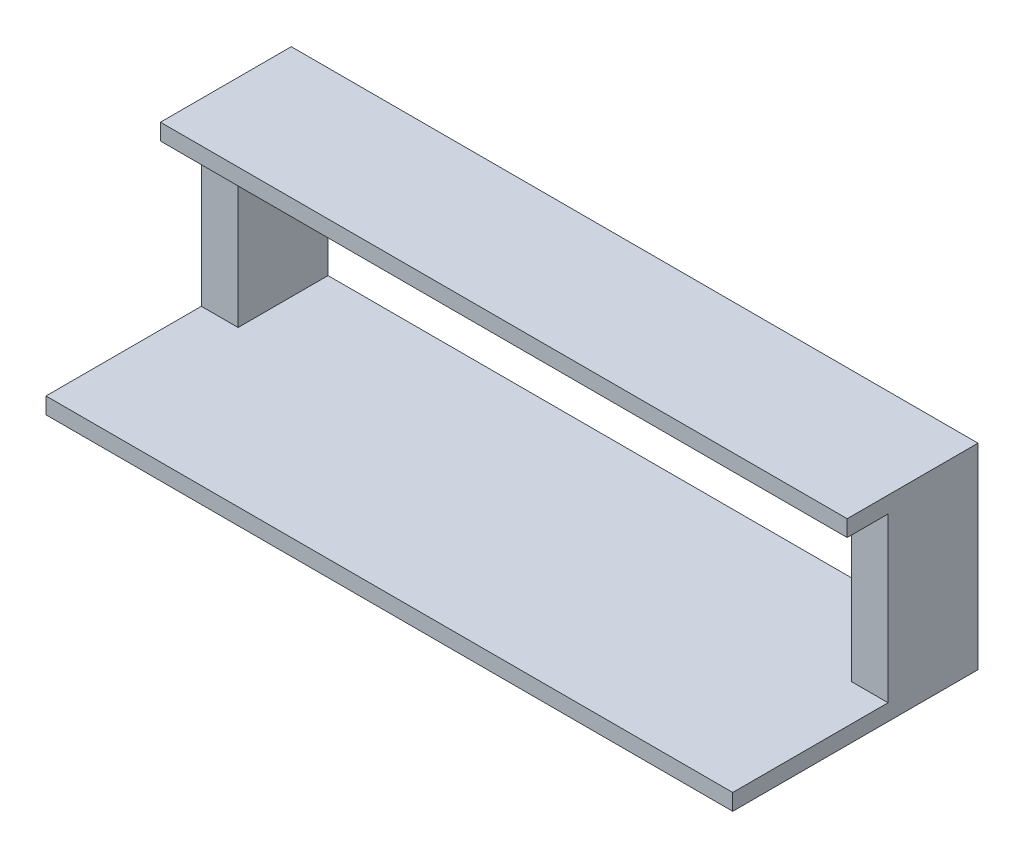
SolidWorks part; units mm, degrees
ref_plane "Front Plane" through (0, 0, 0) normal (0, 0, 1) x (1, 0, 0)
ref_plane "Top Plane" through (0, 0, 0) normal (0, 1, 0) x (1, 0, 0)
ref_plane "Right Plane" through (0, 0, 0) normal (1, 0, 0) x (0, 0, -1)
sketch "Sketch1" plane through (0, 0, 0) normal (0, 1, 0) x (1, 0, 0)
  line L1 (-1066.8, -381) -> (1066.8, -381)
  line L2 (-1066.8, -381) -> (-1066.8, 381)
  line L3 (-1066.8, 381) -> (1066.8, 381)
  line L4 (1066.8, -381) -> (1066.8, 381)
  line L5 (-1066.8, -381) -> (1066.8, 381) construction
  line L6 (-1066.8, 381) -> (1066.8, -381) construction
  point P0 (0, 0)
  dimension "D1" = 2133.6
  dimension "D2" = 762
extrude "Boss-Extrude1" add sketch "Sketch1" along normal blind 50.8
sketch "Sketch3" plane through (0, 50.8, 0) normal (0, 1, 0) x (1, 0, 0)
  line L1 (-1066.8, 381) -> (-952.5, 381)
  line L2 (-1066.8, 381) -> (-1066.8, 101.6)
  line L3 (-1066.8, 101.6) -> (-952.5, 101.6)
  line L4 (-952.5, 381) -> (-952.5, 101.6)
  line L5 (1066.8, 381) -> (952.5, 381)
  line L6 (1066.8, 381) -> (1066.8, 101.6)
  line L7 (1066.8, 101.6) -> (952.5, 101.6)
  line L8 (952.5, 381) -> (952.5, 101.6)
  dimension "D1" = 114.3
  dimension "D2" = 279.4
extrude "Boss-Extrude2" add sketch "Sketch3" along normal blind 508
sketch "Sketch4" plane through (0, 558.8, 0) normal (0, 1, 0) x (1, 0, 0)
  line L1 (-1066.8, 381) -> (1066.8, 381)
  line L2 (-1066.8, 381) -> (-1066.8, 101.6)
  line L3 (-1066.8, 101.6) -> (1066.8, 101.6)
  line L4 (1066.8, 381) -> (1066.8, 101.6)
extrude "Boss-Extrude3" add sketch "Sketch4" along normal blind 50.8
sketch "Sketch5" plane through (0, 0, -101.6) normal (0, 0, 1) x (1, 0, 0)
  line L0 (-952.5, 558.8) -> (952.5, 558.8) construction
  line L1 (-1066.8, 609.6) -> (1066.8, 609.6)
  line L2 (-1066.8, 609.6) -> (-1066.8, 558.8)
  line L3 (-1066.8, 558.8) -> (1066.8, 558.8)
  line L4 (1066.8, 609.6) -> (1066.8, 558.8)
  line L5 (1066.8, 609.6) -> (1066.8, 50.8) construction
extrude "Boss-Extrude4" add sketch "Sketch5" along normal blind 127
